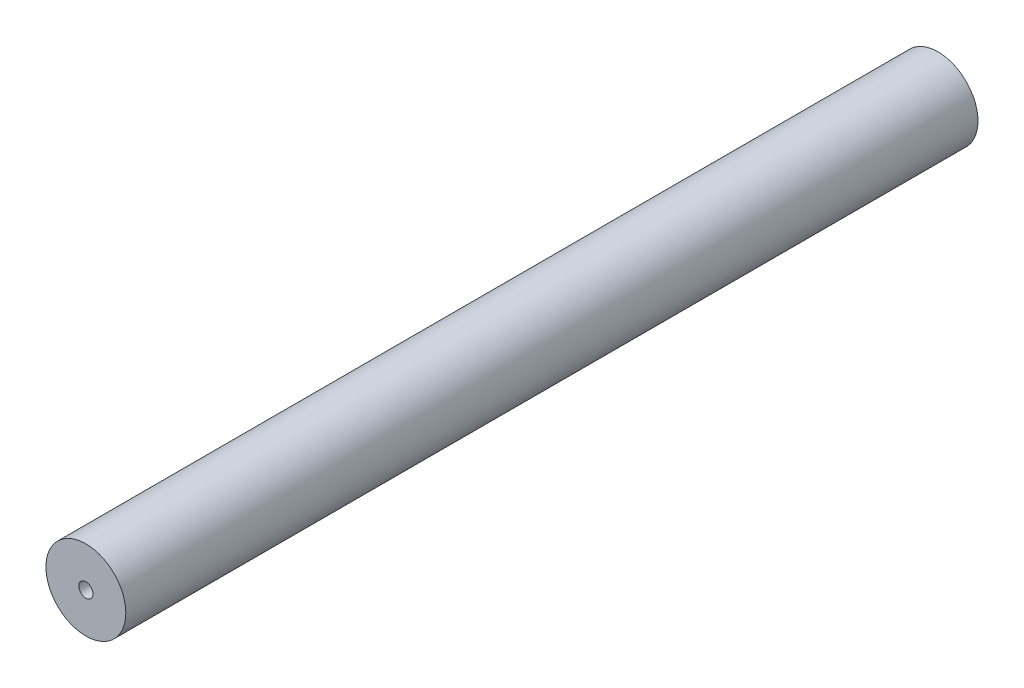
SolidWorks part; units mm, degrees
material "ABS PC"
ref_plane "Front Plane" through (0, 0, 0) normal (0, 0, 1) x (1, 0, 0)
ref_plane "Top Plane" through (0, 0, 0) normal (0, 1, 0) x (1, 0, 0)
ref_plane "Right Plane" through (0, 0, 0) normal (1, 0, 0) x (0, 0, -1)
sketch "Sketch1" plane through (0, 0, 0) normal (0, 0, 1) x (1, 0, 0)
  circle A0 centre (0, 0) radius 2.25
  circle A1 centre (0, 0) radius 0.4
  dimension "D1" = 4.5
  dimension "D2" = 0.8
extrude "Boss-Extrude1" add sketch "Sketch1" along normal blind 48
